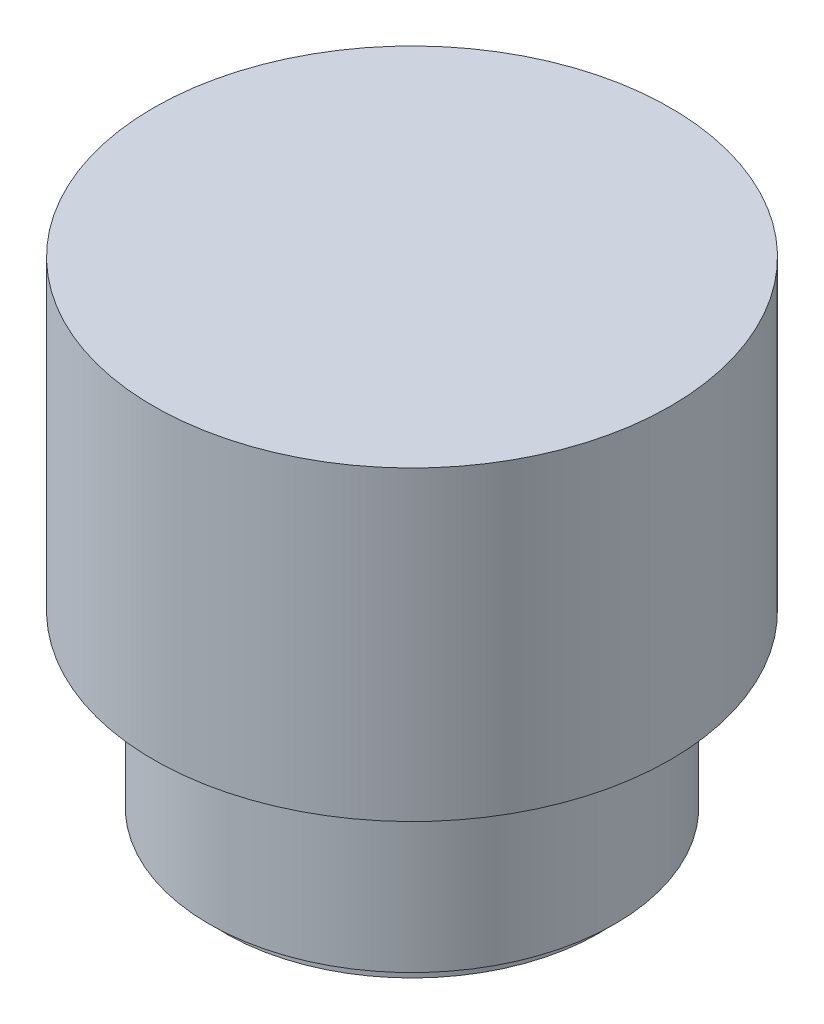
SolidWorks part; units mm, degrees
material "ABS PC"
ref_plane "Front Plane" through (0, 0, 0) normal (0, 0, 1) x (1, 0, 0)
ref_plane "Top Plane" through (0, 0, 0) normal (0, 1, 0) x (1, 0, 0)
ref_plane "Right Plane" through (0, 0, 0) normal (1, 0, 0) x (0, 0, -1)
sketch "Sketch1" plane through (0, 0, 0) normal (0, 0, 1) x (1, 0, 0)
  line L0 (0, -426.0881) -> (0, 20878.3164) construction
  line L1 (0, 0) -> (-23.5, 0)
  line L2 (-23.5, 0) -> (-23.5, 2)
  line L3 (-23.5, 2) -> (-25.5, 2)
  line L4 (-25.5, 2) -> (-25.5, 23.4)
  line L5 (-25.5, 23.4) -> (-32.5, 23.4)
  line L6 (-32.5, 23.4) -> (-32.5, 61.9)
  line L7 (-32.5, 61.9) -> (0, 61.9)
  line L8 (0, 61.9) -> (0, 0)
  dimension "D1" = 51
  dimension "D2" = 65
  dimension "D3" = 61.9
  dimension "D4" = 38.5
  dimension "D5" = 2
  dimension "D6" = 2
revolve "Revolve1" add sketch "Sketch1" angle 360 about L0
ref_plane "Plane2" through (0, 41.5, 0) normal (0, -1, 0) x (-1, 0, 0)
sketch "Sketch2" plane through (0, 41.5, 0) normal (0, -1, 0) x (-1, 0, 0)
  line L0 (-19.9299, 32.5) -> (-19.85, 14.195)
  line L1 (-19.85, 14.195) -> (-13.5, 14.195)
  line L2 (-13.5, 14.195) -> (-13.5, 32.5)
  line L3 (-13.5, 32.5) -> (-19.9299, 32.5)
  line L4 (-13.5, -985.805) -> (-13.5, 49014.195) construction
  circle A0 centre (0, 0) radius 32.5 construction
  point P10 (-19.9002, 25.695)
  dimension "D1" = 12.7
  dimension "D2" = 13.5
  dimension "D3" = 0.25
  dimension "D4" = 11.5
revolve "Cut-Revolve1" cut sketch "Sketch2" angle 360 about L4
mirror "Mirror1" about plane through (0, 0, 0) normal (1, 0, 0) of "Cut-Revolve1"
sketch "Sketch3" plane through (0, 0, 0) normal (0, -1, 0) x (1, 0, 0)
  line L1 (15, 15) -> (-15, 15) construction
  line L2 (15, 15) -> (15, -15) construction
  line L3 (15, -15) -> (-15, -15) construction
  line L4 (-15, 15) -> (-15, -15) construction
  line L5 (15, 15) -> (-15, -15) construction
  line L6 (15, -15) -> (-15, 15) construction
  circle A0 centre (-15, 15) radius 1.25
  circle A1 centre (-15, -15) radius 1.25
  circle A2 centre (15, -15) radius 1.25
  circle A3 centre (15, 15) radius 1.25
  point P0 (0, 0)
  dimension "D2" = 2.5
  dimension "D1" = 30
extrude "Cut-Extrude1" cut sketch "Sketch3" against normal blind 8
